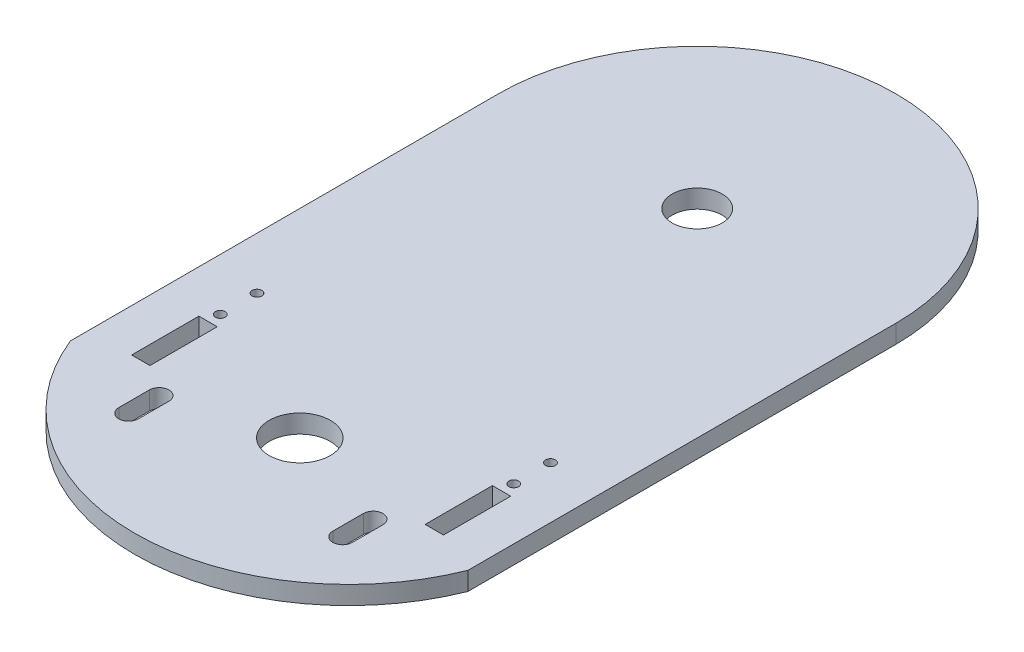
SolidWorks part; units mm, degrees
ref_plane "Front Plane" through (0, 0, 0) normal (0, 0, 1) x (1, 0, 0)
ref_plane "Top Plane" through (0, 0, 0) normal (0, 1, 0) x (1, 0, 0)
ref_plane "Right Plane" through (0, 0, 0) normal (1, 0, 0) x (0, 0, -1)
sketch "Sketch1" plane through (0, 0, 0) normal (0, 1, 0) x (1, 0, 0)
  line L1 (-32.5, -35) -> (32.5, -35)
  line L2 (-32.5, -35) -> (-32.5, 35)
  line L3 (-32.5, 35) -> (32.5, 35)
  line L4 (32.5, -35) -> (32.5, 35)
  line L5 (-32.5, -35) -> (32.5, 35) construction
  line L6 (-32.5, 35) -> (32.5, -35) construction
  arc A0 (-32.5, 35) -> (32.5, 35) centre (0, 35) cw
  arc A1 (32.5, -35) -> (-32.5, -35) centre (0, -22.0096) cw
  point P0 (0, 0)
  dimension "D3" = 35
  dimension "D1" = 65
  dimension "D2" = 70
extrude "Boss-Extrude1" add sketch "Sketch1" along normal blind 3
sketch "Sketch2" plane through (0, 3, 0) normal (0, 1, 0) x (1, 0, 0)
  line L0 (0, 35) -> (0, -32.0878) construction
  line L1 (-32.5, -38) -> (32.5, -38) construction
  line L2 (-32.5, -35) -> (-32.5, 35) construction
  line L3 (32.5, -35) -> (32.5, 35) construction
  circle A0 centre (0, 35) radius 4.1
  circle A1 centre (0, -30) radius 5
  circle A2 centre (-17.5, -38) radius 1.6
  circle A3 centre (17.5, -38) radius 1.6
  dimension "D1" = 8.2
  dimension "D2" = 10
  dimension "D3" = 8
  dimension "D4" = 35
  dimension "D5" = 3.2
  dimension "D6" = 65
extrude "Cut-Extrude1" cut sketch "Sketch2" against normal through all
sketch "Sketch3" plane through (0, 3, 0) normal (0, 1, 0) x (1, 0, 0)
  line L0 (-32.5, -16) -> (31.9496, -16) construction
  line L1 (-32.5, -35) -> (-32.5, 35) construction
  line L2 (0, -25) -> (0, -6.5279) construction
  line L3 (25.5, -32) -> (22.5, -32)
  line L4 (-25.5, -21) -> (-22.5, -21)
  line L5 (-25.5, -21) -> (-25.5, -32)
  line L6 (-25.5, -32) -> (-22.5, -32)
  line L7 (-22.5, -21) -> (-22.5, -32)
  line L8 (25.5, -21) -> (25.5, -32)
  line L9 (25.5, -21) -> (22.5, -21)
  line L10 (22.5, -21) -> (22.5, -32)
  line L11 (-24, -21) -> (-24, -3.9594) construction
  line L12 (24, -21) -> (24, -3.9594) construction
  circle A0 centre (0, -30) radius 5 construction
  circle A1 centre (-24, -13) radius 0.8
  circle A2 centre (-24, -19) radius 0.8
  circle A3 centre (24, -19) radius 0.8
  circle A4 centre (24, -13) radius 0.8
  dimension "D6" = 1.6
  dimension "D7" = 3
  dimension "D8" = 1.6
  dimension "D9" = 3
  dimension "D1" = 19
  dimension "D2" = 3
  dimension "D3" = 11
  dimension "D4" = 7
  dimension "D5" = 5
extrude "Cut-Extrude2" cut sketch "Sketch3" against normal through all
sketch "Sketch4" plane through (0, 3, 0) normal (0, 1, 0) x (1, 0, 0)
  line L0 (0, -28.1941) -> (0, -48.1191) construction
  line L1 (-17.5, -38) -> (-17.5, -28.1941) construction
  line L2 (-17.5, -35.5) -> (-17.5, -40.5) construction
  line L3 (-15.9, -35.5) -> (-15.9, -40.5)
  line L4 (-19.1, -35.5) -> (-19.1, -40.5)
  line L5 (17.5, -35.5) -> (17.5, -40.5) construction
  line L6 (15.9, -35.5) -> (15.9, -40.5)
  line L7 (19.1, -35.5) -> (19.1, -40.5)
  arc A0 (-15.9, -35.5) -> (-19.1, -35.5) centre (-17.5, -35.5) ccw
  arc A1 (-19.1, -40.5) -> (-15.9, -40.5) centre (-17.5, -40.5) ccw
  arc A2 (15.9, -35.5) -> (19.1, -35.5) centre (17.5, -35.5) cw
  arc A3 (19.1, -40.5) -> (15.9, -40.5) centre (17.5, -40.5) cw
  point P8 (-17.5, -38)
  point P15 (17.5, -38)
  dimension "D1" = 1.6
  dimension "D2" = 2.5
  dimension "D3" = 2.5
extrude "Cut-Extrude3" cut sketch "Sketch4" against normal through all
